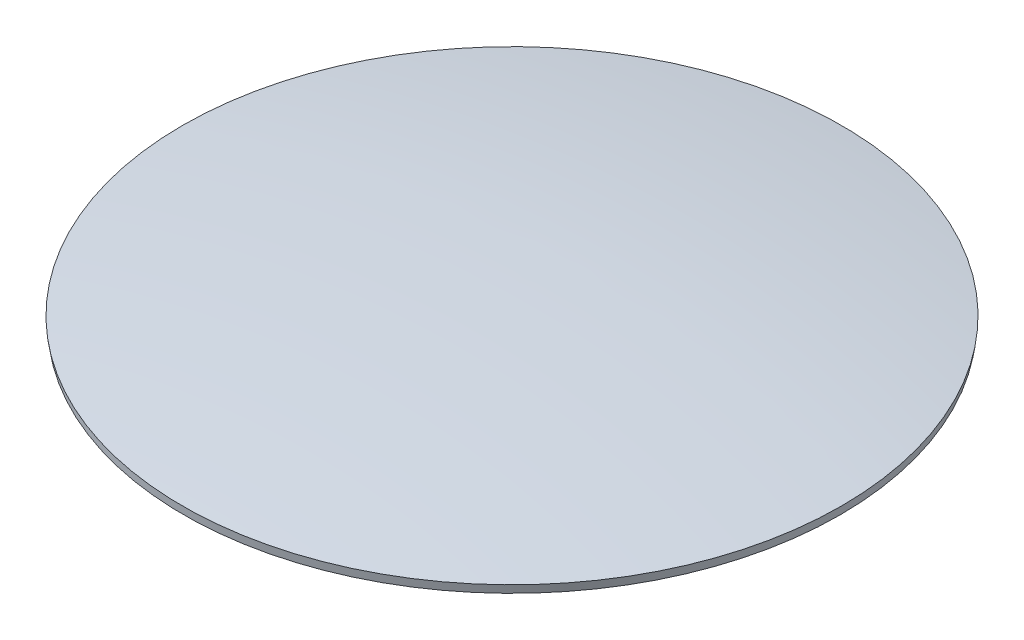
SolidWorks part; units mm, degrees
ref_plane "Face" through (0, 0, 0) normal (0, 0, 1) x (1, 0, 0)
ref_plane "Dessus" through (0, 0, 0) normal (0, 1, 0) x (1, 0, 0)
ref_plane "Droite" through (0, 0, 0) normal (1, 0, 0) x (0, 0, -1)
sketch "Esquisse1" plane through (0, 0, 0) normal (0, 0, 1) x (1, 0, 0)
  line L0 (0, 2) -> (0, 0) construction
  line L1 (0, 2) -> (7.0186, 2) construction
  line L2 (-19.5, 0.4941) -> (-19.4232, 0)
  line L3 (-19.4232, 0) -> (0, 0) construction
  line L4 (0, 2) -> (0, 1.5)
  arc A0 (0, 2) -> (-19.5, 0.4941) centre (0, -125.004) ccw
  arc A1 (0, 1.5) -> (-19.4232, 0) centre (0, -125.004) ccw
  dimension "D2" = 19.5
  dimension "D3" = 2
  dimension "D1" = 0.5
revolve "Révolution1" add sketch "Esquisse1" angle 360 about L4
